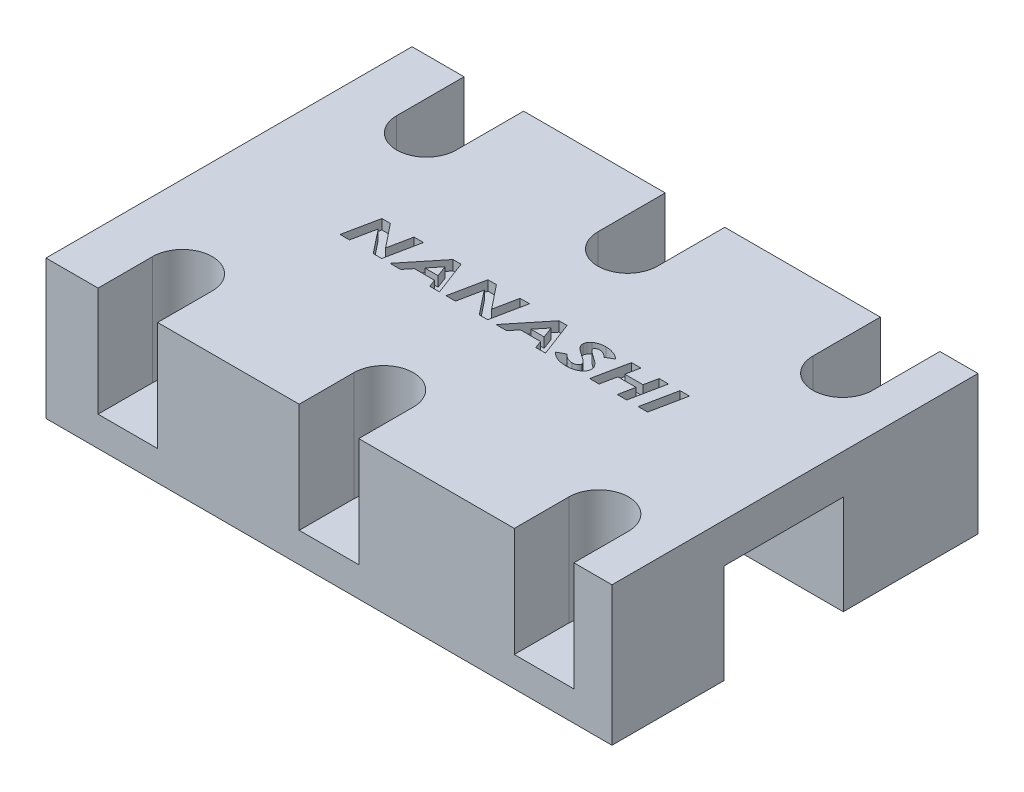
SolidWorks part; units mm, degrees
ref_plane "Front Plane" through (0, 0, 0) normal (0, 0, 1) x (1, 0, 0)
ref_plane "Top Plane" through (0, 0, 0) normal (0, 1, 0) x (1, 0, 0)
ref_plane "Right Plane" through (0, 0, 0) normal (1, 0, 0) x (0, 0, -1)
sketch "Sketch1" plane through (0, 0, 0) normal (0, 1, 0) x (1, 0, 0)
sketch "Sketch2" plane through (0, 54.654, 0) normal (0, 1, 0) x (1, 0, 0)
  line L5 (0.0616, -71.6434) -> (0.0616, -34.7834) construction
  line L6 (0.0616, -60.3519) -> (57.0616, -60.3519)
  line L7 (0.0616, -60.3519) -> (0.0616, -71.6434)
  line L8 (0.0616, -71.6434) -> (57.0616, -71.6434)
  line L9 (57.0616, -60.3519) -> (57.0616, -71.6434)
  line L10 (-1.0884, -60.3519) -> (9.7616, -60.3519) construction
  line L11 (9.7616, -48.3519) -> (-1.0884, -48.3519) construction
  line L12 (0.0616, -48.3519) -> (57.0616, -48.3519)
  line L13 (0.0616, -48.3519) -> (0.0616, -34.7834)
  line L14 (0.0616, -34.7834) -> (57.0616, -34.7834)
  line L15 (57.0616, -48.3519) -> (57.0616, -34.7834)
extrude "Boss-Extrude2" add sketch "Sketch2" along normal up to surface (10 mm away)
sketch "Sketch5" plane through (0, 64.654, 0) normal (0, 1, 0) x (1, 0, 0)
  line L1 (0.0616, -34.7834) -> (57.0616, -34.7834)
  line L2 (0.0616, -34.7834) -> (0.0616, -48.3519)
  line L3 (0.0616, -48.3519) -> (57.0616, -48.3519)
  line L4 (57.0616, -34.7834) -> (57.0616, -48.3519)
  line L5 (0.0616, -60.3519) -> (57.0616, -60.3519)
  line L6 (0.0616, -60.3519) -> (0.0616, -71.6434)
  line L7 (0.0616, -71.6434) -> (57.0616, -71.6434)
  line L8 (57.0616, -60.3519) -> (57.0616, -71.6434)
  point P14 (0, 0)
  point P15 (28.6079, -41.9867)
extrude "Boss-Extrude7" add sketch "Sketch5" along normal blind 4
sketch "Sketch13" plane through (0, 0, 48.3519) normal (0, 0, 1) x (1, 0, 0)
  line L0 (57.0616, 68.654) -> (57.0616, 54.654) construction
  line L1 (0.0616, 68.654) -> (57.0616, 68.654)
  line L2 (0.0616, 68.654) -> (0.0616, 64.654)
  line L3 (0.0616, 64.654) -> (57.0616, 64.654)
  line L4 (57.0616, 68.654) -> (57.0616, 64.654)
  dimension "D1" = 4
extrude "Boss-Extrude8" add sketch "Sketch13" along normal up to surface (12 mm away) up to face at (28.5616, 61.654, 60.3519)
sketch "Sketch15" plane through (0, 68.654, 0) normal (0, 1, 0) x (1, 0, 0)
  line L0 (57.2048, -48.3519) -> (-0.2319, -48.3519) construction
  line L1 (58.2116, -48.3519) -> (47.3616, -48.3519) construction
  line L2 (9.7616, -48.3519) -> (-1.0884, -48.3519) construction
  line L3 (57.0616, -60.3519) -> (0.0616, -60.3519) construction
  line L4 (57.0616, -34.7834) -> (0.0616, -34.7834) construction
  line L5 (57.0616, -71.6434) -> (57.0616, -34.7834) construction
  line L6 (0.0616, -71.6434) -> (57.0616, -71.6434) construction
  circle A0 centre (28.5616, -41.5684) radius 1.45
  circle A1 centre (50.224, -41.5684) radius 1.45
  circle A2 centre (8.3042, -41.5684) radius 1.45
  circle A3 centre (8.3042, -66.1434) radius 1.45
  circle A4 centre (28.5616, -66.1434) radius 1.45
  circle A5 centre (50.224, -66.1434) radius 1.45
  dimension "D1" = 2.9
  dimension "D3" = 28.5
  dimension "D2" = 6.785
  dimension "2.9" = 5.5
extrude "Cut-Extrude1" cut sketch "Sketch15" against normal through all
sketch "Sketch16" plane through (0, 68.654, 0) normal (0, 1, 0) x (1, 0, 0)
  line L0 (57.0616, -34.7834) -> (0.0616, -34.7834) construction
  line L2 (5.3042, -41.5684) -> (5.3042, -34.7834)
  line L3 (5.3042, -34.7834) -> (11.3042, -34.7834)
  line L4 (11.3042, -41.5684) -> (11.3042, -34.7834)
  line L5 (0.0616, -71.6434) -> (57.0616, -71.6434) construction
  line L7 (25.5616, -41.5684) -> (25.5616, -34.7834)
  line L8 (25.5616, -34.7834) -> (31.5616, -34.7834)
  line L9 (31.5616, -41.5684) -> (31.5616, -34.7834)
  line L11 (47.224, -41.5684) -> (47.224, -34.7834)
  line L12 (47.224, -34.7834) -> (53.224, -34.7834)
  line L13 (53.224, -41.5684) -> (53.224, -34.7834)
  line L15 (47.224, -66.1434) -> (47.224, -71.6434)
  line L16 (47.224, -71.6434) -> (53.224, -71.6434)
  line L17 (53.224, -66.1434) -> (53.224, -71.6434)
  line L20 (25.5616, -66.1434) -> (25.5616, -71.6434)
  line L21 (25.5616, -71.6434) -> (31.5616, -71.6434)
  line L22 (31.5616, -66.1434) -> (31.5616, -71.6434)
  line L24 (5.3042, -66.1434) -> (5.3042, -71.6434)
  line L25 (5.3042, -71.6434) -> (11.3042, -71.6434)
  line L26 (11.3042, -66.1434) -> (11.3042, -71.6434)
  arc A0 (5.3042, -41.5684) -> (11.3042, -41.5684) centre (8.3042, -41.5684) ccw
  arc A1 (25.5616, -41.5684) -> (31.5616, -41.5684) centre (28.5616, -41.5684) ccw
  arc A2 (47.224, -41.5684) -> (53.224, -41.5684) centre (50.224, -41.5684) ccw
  arc A3 (11.3042, -66.1434) -> (5.3042, -66.1434) centre (8.3042, -66.1434) ccw
  arc A4 (31.5616, -66.1434) -> (25.5616, -66.1434) centre (28.5616, -66.1434) ccw
  arc A5 (53.224, -66.1434) -> (47.224, -66.1434) centre (50.224, -66.1434) ccw
  dimension "D1" = 6
  dimension "D2" = 6
  dimension "D3" = 6
  dimension "D4" = 6
  dimension "D5" = 6
  dimension "D6" = 6
extrude "Cut-Extrude3" cut sketch "Sketch16" against normal blind 11
sketch "Sketch17" plane through (0, 68.654, 0) normal (0, 1, 0) x (1, 0, 0)
  text T1 "<b>NANASHI</b>" font "Century Gothic" height 3.5
extrude "Cut-Extrude4" cut sketch "Sketch17" against normal blind 1
